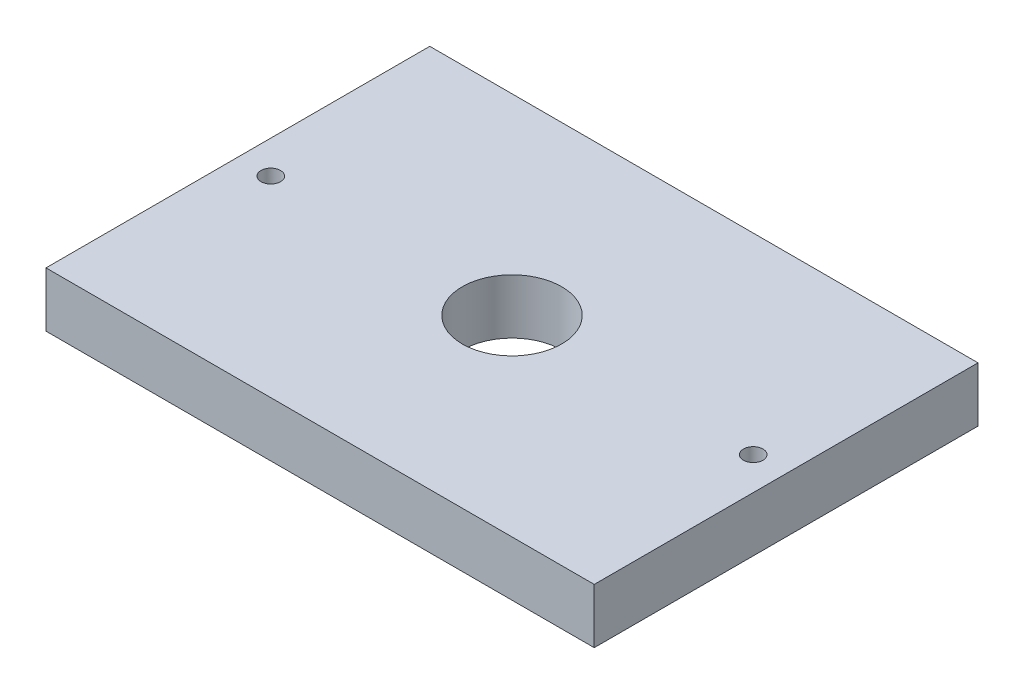
SolidWorks part; units mm, degrees
ref_plane "Front Plane" through (0, 0, 0) normal (0, 0, 1) x (1, 0, 0)
ref_plane "Top Plane" through (0, 0, 0) normal (0, 1, 0) x (1, 0, 0)
ref_plane "Right Plane" through (0, 0, 0) normal (1, 0, 0) x (0, 0, -1)
sketch "Sketch1" plane through (0, 0, 0) normal (0, 1, 0) x (1, 0, 0)
  line L1 (-26.9974, 3.2608) -> (36.5026, 3.2608)
  line L2 (-26.9974, 3.2608) -> (-26.9974, -41.1892)
  line L3 (-26.9974, -41.1892) -> (36.5026, -41.1892)
  line L4 (36.5026, 3.2608) -> (36.5026, -41.1892)
  dimension "D1" = 44.45
  dimension "D2" = 63.5
extrude "Boss-Extrude1" add sketch "Sketch1" along normal blind 6.35
hole_wizard "Tap Drill for #4-40 Tap1" positions "Sketch17" profile "Sketch16" hole size "#4-40" standard "Ansi Inch"
sketch "Sketch17" plane through (0, 0, 0) normal (0, -1, 0) x (1, 0, 0)
  line L0 (-26.9974, 41.1892) -> (36.5026, 41.1892) construction
  line L1 (-26.9974, -3.2608) -> (-26.9974, 41.1892) construction
  point P0 (-23.1874, 18.9642)
  dimension "D1" = 22.225
  dimension "D2" = 3.81
sketch "Sketch16" plane through (-23.1874, 0, 18.9642) normal (1, 0, 0) x (0, 0, -1)
  line L0 (0, 0) -> (0, 13.3792)
  line L1 (0, 13.3792) -> (1.1303, 12.7)
  line L2 (1.1303, 12.7) -> (1.1303, 0)
  line L5 (1.1303, 0) -> (0, 0)
  line L10 (0, 13.3792) -> (-1.1303, 12.7) construction
  line L11 (0, -6.35) -> (0, 107.95) construction
  dimension "Hole Dia." = 2.2606
  dimension "Hole Depth" = 12.7
  dimension "Drill Angle" = 118
pattern_linear "LPattern1" count 2 spacing 55.88 along (1, 0, 0) of "Tap Drill for #4-40 Tap1"
hole_wizard "Tap Drill for 1/2-20 Tap1" positions "Sketch27" profile "Sketch26" hole size "1/2-20" standard "Ansi Inch"
sketch "Sketch27" plane through (0, 6.35, 0) normal (0, 1, 0) x (-1, 0, 0)
  line L0 (26.9974, -3.2608) -> (26.9974, 41.1892) construction
  line L1 (26.9974, 41.1892) -> (-36.5026, 41.1892) construction
  point P0 (-4.7526, 18.9642)
  dimension "D1" = 31.75
  dimension "D2" = 22.225
sketch "Sketch26" plane through (4.7526, 6.35, 18.9642) normal (1, 0, 0) x (0, 0, 1)
  line L0 (0, 0) -> (0, 9.8076)
  line L1 (0, 9.8076) -> (5.7544, 6.35)
  line L2 (5.7544, 6.35) -> (5.7544, 0)
  line L5 (5.7544, 0) -> (0, 0)
  line L10 (0, 9.8076) -> (-5.7544, 6.35) construction
  line L11 (0, -6.35) -> (0, 107.95) construction
  dimension "Hole Dia." = 11.5087
  dimension "Hole Depth" = 6.35
  dimension "Drill Angle" = 118
equation "\"D1@Sketch27\" = \"D2@Sketch1\"/2"
equation "\"D1@Sketch17\" = \"D1@Sketch1\"/2"
equation "\"D2@Sketch17\" = (\"D2@Sketch1\"-\"RD2@Annotations\")/2"
equation "\"D2@Sketch27\" = \"D1@Sketch1\"/2"
